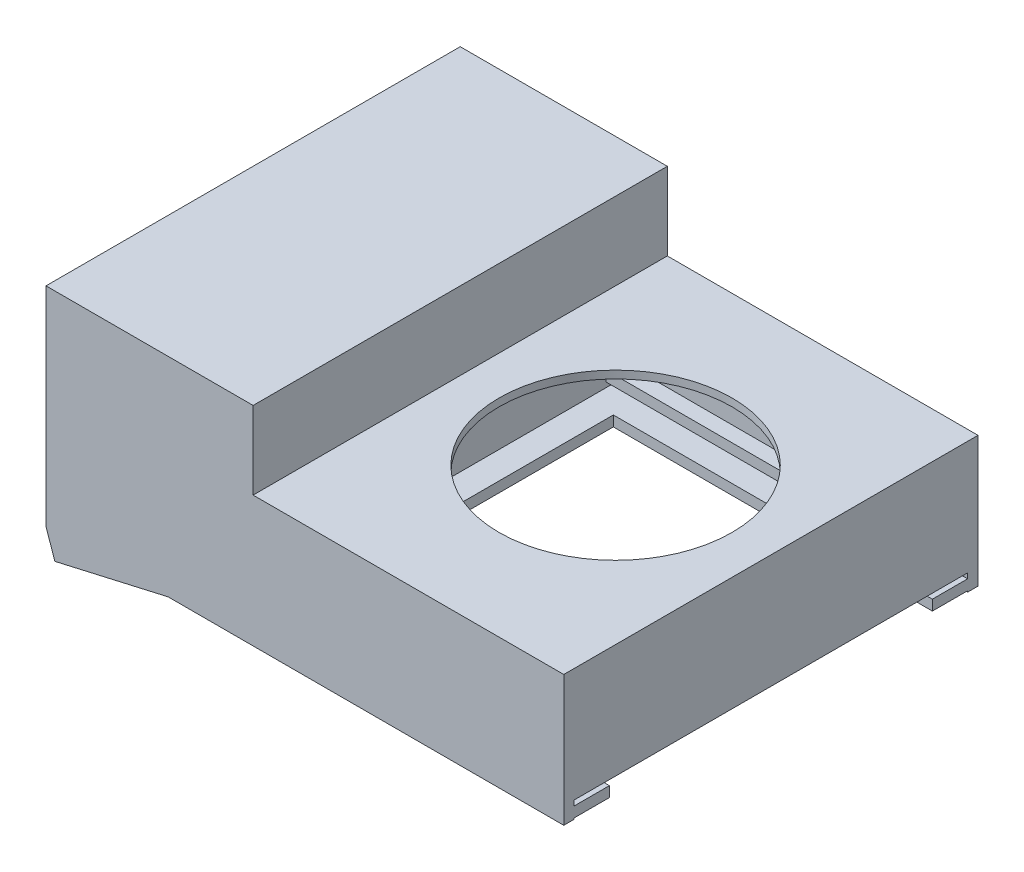
SolidWorks part; units mm, degrees
ref_plane "Front Plane" through (0, 0, 0) normal (0, 0, 1) x (1, 0, 0)
ref_plane "Top Plane" through (0, 0, 0) normal (0, 1, 0) x (1, 0, 0)
ref_plane "Right Plane" through (0, 0, 0) normal (1, 0, 0) x (0, 0, -1)
sketch "Sketch1" plane through (0, 0, 0) normal (0, 0, 1) x (1, 0, 0)
  line L0 (33.4827, -45.2515) -> (33.4827, -66.7685)
  line L1 (-64.5173, -28.7685) -> (-24.5173, -28.7685)
  line L2 (-64.5173, -28.7685) -> (-64.5173, -68.7685)
  line L3 (-64.5173, -68.7685) -> (-62.013, -68.7685)
  line L4 (35.4827, -43.7685) -> (35.4827, -68.7685)
  line L5 (-24.5173, -28.7685) -> (-24.5173, -43.7685)
  line L6 (-62.5173, -66.7685) -> (-62.013, -66.7685)
  line L7 (-31.3941, -66.7685) -> (33.4827, -66.7685)
  line L8 (-24.5173, -43.7685) -> (35.4827, -43.7685)
  line L9 (35.4827, -43.7685) -> (35.7775, -43.6055)
  line L10 (33.4827, -45.2515) -> (-27.3831, -45.2515)
  line L11 (-31.3941, -53.7685) -> (-54.6549, -68.7685)
  line L13 (-62.013, -68.7685) -> (-62.013, -63.1718)
  line L14 (-62.013, -63.1718) -> (-27.3831, -45.2515)
  line L15 (-31.3941, -53.7685) -> (-31.3941, -66.7685)
  line L16 (-62.5173, -66.7685) -> (33.4827, -66.7685) construction
  line L17 (-26.5173, -30.7685) -> (-26.5173, -43.7685) construction
  line L18 (-62.5173, -30.7685) -> (-26.5173, -30.7685) construction
  line L19 (-62.5173, -30.7685) -> (-62.5173, -66.7685) construction
  line L20 (-54.6549, -68.7685) -> (35.4827, -68.7685)
  line L21 (33.4827, -43.7685) -> (33.4827, -66.7685) construction
  line L23 (-64.5173, -68.7685) -> (35.4827, -68.7685) construction
  dimension "D1" = 2
extrude "Boss-Extrude1" add sketch "Sketch1" along normal blind 80
sketch "Sketch4" plane through (0, -43.7685, 0) normal (0, 1, 0) x (1, 0, 0)
  line L0 (-31.3941, -40) -> (-31.3941, -55)
  line L3 (-31.3941, -80) -> (-31.3941, 0) construction
  line L5 (-54.6549, -80) -> (-31.3941, -55)
  line L6 (-31.3941, -40) -> (-36.3955, -40)
  line L7 (-54.6549, -80) -> (-31.3941, -80)
  line L8 (-64.5173, -80) -> (-24.5173, -80) construction
  line L9 (-31.3941, -80) -> (-31.3941, -55)
  line L10 (-31.3941, 0) -> (-31.3941, -25)
  line L11 (-54.6549, 0) -> (-31.3941, 0)
  line L12 (-54.6549, 0) -> (-31.3941, -25)
extrude "Boss-Extrude2" add sketch "Sketch4" against normal blind 25 contours L7 L9 L5 | L11 L12 L10
sketch "Sketch5" plane through (0, 0, 0) normal (0, 1, 0) x (1, 0, 0)
  line L0 (-64.5173, -80) -> (-24.5173, -80) construction
  line L1 (-64.5173, -80) -> (35.4827, -80)
  line L2 (-64.5173, -80) -> (-64.5173, -78)
  line L3 (-64.5173, -78) -> (35.4827, -78)
  line L4 (35.4827, -80) -> (35.4827, -78)
  line L5 (35.4827, -80) -> (35.4827, 0) construction
  line L6 (35.4827, -40) -> (28.8744, -40)
  line L7 (35.4827, 0) -> (35.4827, -2)
  line L8 (-64.5173, -2) -> (35.4827, -2)
  line L9 (-64.5173, 0) -> (-64.5173, -2)
  line L10 (-64.5173, 0) -> (35.4827, 0)
extrude "Boss-Extrude3" add sketch "Sketch5" against normal blind 69 and the other way blind 1 contours L1 L4 L3 L2 | L10 L9 L8 L7
sketch "Sketch6" plane through (0, 0, 0) normal (0, 0, -1) x (-1, 0, 0)
  line L0 (64.5173, -28.7685) -> (24.5173, -28.7685)
  line L1 (24.5173, -28.7685) -> (24.5173, -43.7685)
  line L2 (24.5173, -43.7685) -> (-35.4827, -43.7685)
  line L3 (-35.4827, -43.7685) -> (-64.96, 15.6912)
  line L4 (-64.96, 15.6912) -> (80.8201, 20.7033)
  line L5 (80.8201, 20.7033) -> (64.5173, -28.7685)
extrude "Cut-Extrude1" cut sketch "Sketch6" against normal blind 128 and the other way blind 54
sketch "Sketch7" plane through (0, 0, 80) normal (0, 0, 1) x (1, 0, 0)
  line L0 (-52.7941, -67.5685) -> (-62.8145, -74)
  line L1 (-64.1776, -69) -> (-64.1776, -74)
  line L2 (-64.5173, -69) -> (35.4827, -69) construction
  line L3 (-52.7941, -67.5685) -> (-47.2805, -68.0087)
  line L4 (-47.2805, -68.0087) -> (-39.3685, -68.6403)
  line L5 (-39.3685, -68.6403) -> (-62.8145, -74)
  line M7 (-64.5173, -69) -> (35.4827, -69)
extrude "Boss-Extrude4" add sketch "Sketch7" against normal blind 80 contours L5 L0 M7 | L5 L4 L3 L0 M7
sketch "Sketch9" plane through (0, 0, 80) normal (0, 0, 1) x (1, 0, 0)
  line L0 (-64.5173, -69) -> (-55.0244, -69)
  line L1 (-55.0244, -69) -> (-62.8145, -74)
  line L2 (-62.8145, -74) -> (-64.5173, -69)
extrude "Boss-Extrude5" add sketch "Sketch9" against normal blind 2
sketch "Sketch10" plane through (0, 0, 0) normal (0, 0, -1) x (-1, 0, 0)
  line L0 (64.5173, -69) -> (55.0244, -69)
  line L1 (55.0244, -69) -> (62.8145, -74)
  line L2 (62.8145, -74) -> (64.5173, -69)
extrude "Boss-Extrude6" add sketch "Sketch10" against normal blind 2
sketch "Sketch11" plane through (0, -43.7685, 0) normal (0, 1, 0) x (1, 0, 0)
  line L0 (35.4827, -40) -> (-24.5173, -40)
  line L1 (35.4827, -80) -> (35.4827, 0) construction
  line L2 (-24.5173, -80) -> (-24.5173, 0) construction
  circle A0 centre (5.4827, -40) radius 22.5
extrude "Cut-Extrude2" cut sketch "Sketch11" against normal blind 10 contours L0 A0 | L0 A0
sketch "Sketch12" plane through (0, 0, 78) normal (0, 0, -1) x (-1, 0, 0)
  line L0 (31.3941, -66.7685) -> (31.3941, -65.7685)
  line L1 (31.3941, -66.7685) -> (31.3941, -47.3271) construction
  line L3 (31.3941, -65.7685) -> (-35.2324, -65.7685)
  line L4 (31.3941, -65.7685) -> (31.3941, -63.7685)
  line L5 (31.3941, -63.7685) -> (-35.2324, -63.7685)
  line L6 (-35.2324, -65.7685) -> (-35.2324, -63.7685)
extrude "Boss-Extrude7" add sketch "Sketch12" along normal blind 3 contours L4 L5 L6 L3
sketch "Sketch13" plane through (0, 0, 2) normal (0, 0, 1) x (1, 0, 0)
  line L0 (-31.3941, -66.7685) -> (-31.3941, -65.7685)
  line L1 (-31.3941, -66.7685) -> (-31.3941, -47.3271) construction
  line L2 (33.4827, -66.7685) -> (33.4827, -45.2515) construction
  line L3 (-31.3941, -65.7685) -> (33.4827, -65.7685)
  line L4 (-31.3941, -65.7685) -> (-31.3941, -63.7685)
  line L5 (-31.3941, -63.7685) -> (33.4827, -63.7685)
  line L6 (33.4827, -65.7685) -> (33.4827, -63.7685)
extrude "Boss-Extrude8" add sketch "Sketch13" along normal blind 3 contours L4 L5 L6 L3
sketch "Sketch14" plane through (35.4827, 0, 0) normal (1, 0, 0) x (0, 0, -1)
  line L0 (-2, -66.7685) -> (-2, -65.7685) construction
  line L1 (-78, -65.7685) -> (-2, -65.7685)
  line L2 (-78, -65.7685) -> (-78, -66.7685)
  line L3 (-78, -66.7685) -> (-8.8104, -66.7685)
  line L4 (-2, -65.7685) -> (-2, -66.7685)
  line L5 (-78, -66.7685) -> (-2, -66.7685) construction
  line L6 (-8.8104, -66.7685) -> (-2, -66.7685)
  line L7 (-78, -68.7685) -> (-2, -68.7685) construction
  line L8 (-2, -66.7685) -> (-2.0829, -66.7602)
  line L9 (-2, -68.7685) -> (-8.8104, -68.7685)
  line L10 (-2, -66.7685) -> (-2, -68.7685)
  line L11 (-40, -67.5685) -> (-40, -68.7685)
  line L12 (-8.8104, -66.7685) -> (-8.8104, -68.7685)
  line L13 (-2, -67.5685) -> (-78, -67.5685) construction
  line L14 (-71.1896, -66.7685) -> (-78, -66.7685)
  line L15 (-78, -66.7685) -> (-78, -68.7685)
  line L16 (-78, -68.7685) -> (-71.1896, -68.7685)
  line L17 (-71.1896, -66.7685) -> (-71.1896, -68.7685)
extrude "Cut-Extrude3" cut sketch "Sketch14" against normal blind 61.6186
